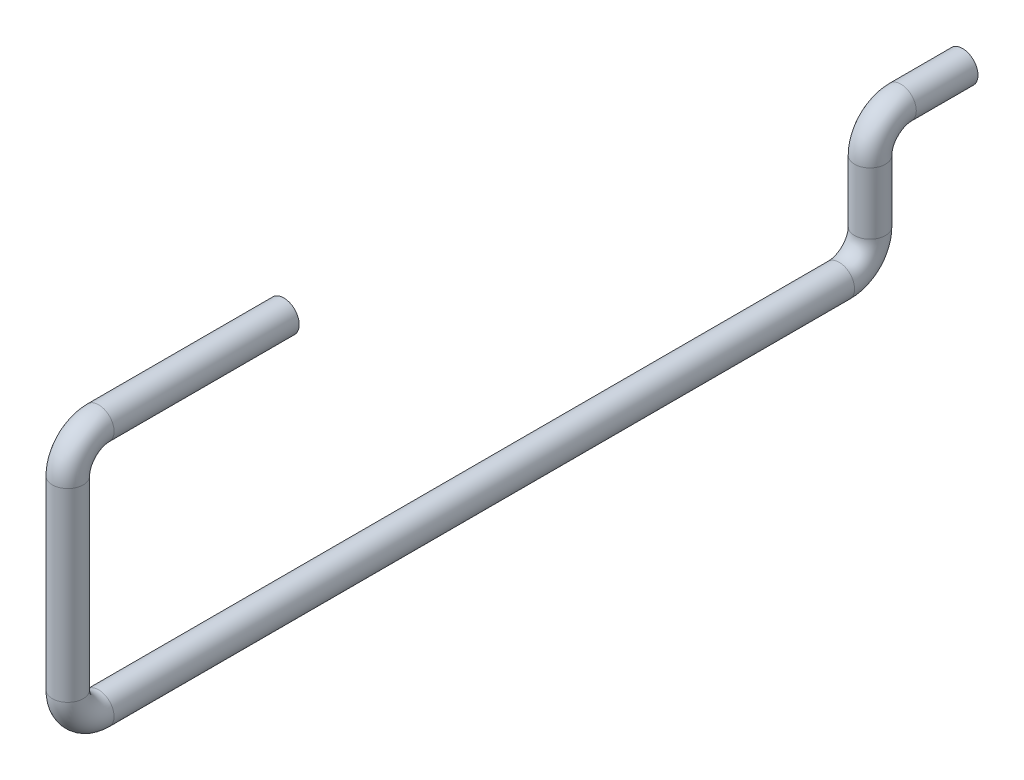
SolidWorks part; units mm, degrees
ref_plane "Front Plane" through (0, 0, 0) normal (0, 0, 1) x (1, 0, 0)
ref_plane "Top Plane" through (0, 0, 0) normal (0, 1, 0) x (1, 0, 0)
ref_plane "Right Plane" through (0, 0, 0) normal (1, 0, 0) x (0, 0, -1)
sketch "Sketch1" plane through (0, 0, 0) normal (1, 0, 0) x (0, 0, -1)
  line L0 (-13, 7) -> (-13, 1)
  line L1 (-12, 0) -> (12, 0)
  line L2 (13, 3) -> (13, 1)
  line L3 (14, 4) -> (16, 4)
  line L4 (-12, 8) -> (-6, 8)
  arc A0 (12, 0) -> (13, 1) centre (12, 1) ccw
  arc A1 (-12, 0) -> (-13, 1) centre (-12, 1) cw
  arc A2 (13, 3) -> (14, 4) centre (14, 3) cw
  arc A3 (-13, 7) -> (-12, 8) centre (-12, 7) cw
  point P8 (13, 4)
  point P11 (-13, 0)
  point P14 (0, 0)
  point P18 (-13, 8)
  point P24 (-13, 8)
  dimension "D4" = 26
  dimension "D5" = 1
  dimension "D6" = 1
  dimension "D2" = 1
  dimension "D1" = 3
  dimension "D3" = 8
  dimension "D7" = 7
sketch "Sketch3" plane through (0, 0, 0) normal (0, 0, 1) x (1, 0, 0)
  circle A0 centre (0, 0) radius 0.5
  dimension "D1" = 1
sweep "Sweep2" add profiles "Sketch3" path "Sketch1"
